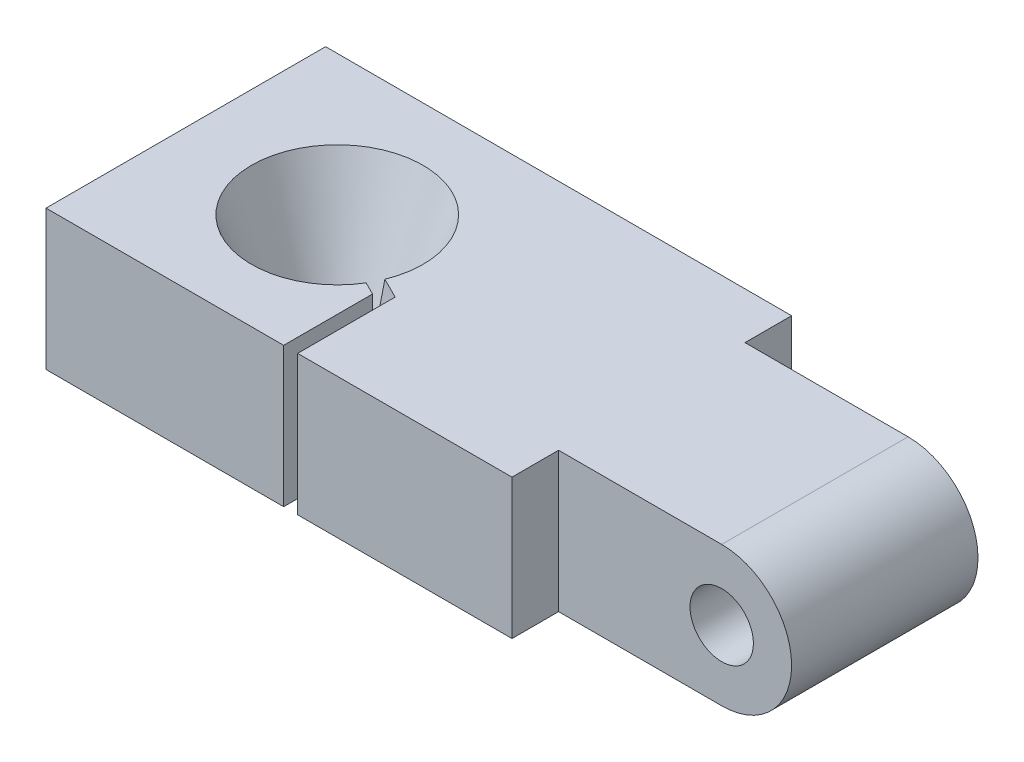
SolidWorks part; units mm, degrees
ref_plane "Front Plane" through (0, 0, 0) normal (0, 0, 1) x (1, 0, 0)
ref_plane "Top Plane" through (0, 0, 0) normal (0, 1, 0) x (1, 0, 0)
ref_plane "Right Plane" through (0, 0, 0) normal (1, 0, 0) x (0, 0, -1)
sketch "Sketch1" plane through (0, 0, 0) normal (0, 0, 1) x (1, 0, 0)
  line L1 (-17.145, -3.81) -> (17.145, -3.81)
  line L2 (-17.145, -3.81) -> (-17.145, 3.81)
  line L3 (-17.145, 3.81) -> (17.145, 3.81)
  line L4 (17.145, -3.81) -> (17.145, 3.81) construction
  line L5 (-17.145, -3.81) -> (17.145, 3.81) construction
  line L6 (-17.145, 3.81) -> (17.145, -3.81) construction
  arc A0 (17.145, 3.81) -> (17.145, -3.81) centre (17.145, 0) cw
  point P0 (0, 0)
  dimension "D1" = 7.62
  dimension "D2" = 34.29
extrude "Boss-Extrude1" add sketch "Sketch1" along normal blind 10.16
hole_wizard "#4 Clearance Hole1" positions "Sketch3" profile "Sketch2" hole size "#4" standard "ANSI Inch" end condition through all
sketch "Sketch3" plane through (0, 0, 10.16) normal (0, 0, 1) x (1, 0, 0)
  point P0 (17.145, 0)
sketch "Sketch2" plane through (17.145, 0, 10.16) normal (1, 0, 0) x (0, -1, 0)
  line L0 (0, 0) -> (0, 10.16)
  line L1 (0, 10.16) -> (1.7272, 10.16)
  line L2 (1.7272, 10.16) -> (1.7272, 0)
  line L5 (1.7272, 0) -> (0, 0)
  line L11 (0, -6.35) -> (0, 107.95) construction
  dimension "Thru Hole Dia." = 3.4544
  dimension "Thru Hole Depth" = 10.16
sketch "Sketch4" plane through (0, -3.81, 0) normal (0, 1, 0) x (1, 0, 0)
  line L0 (-17.145, -10.16) -> (-17.145, 0) construction
  circle A0 centre (-8.89, -5.08) radius 1.905
  point P0 (-8.89, -5.08)
  dimension "D2" = 3.81
  dimension "D1" = 8.255
extrude "Cut-Extrude1" cut sketch "Sketch4" along normal through all draft 20 draft outward yes
sketch "Sketch5" plane through (0, -3.81, 0) normal (0, -1, 0) x (1, 0, 0)
  circle A0 centre (-8.89, 5.08) radius 4.1275
  dimension "D1" = 8.255
extrude "Cut-Extrude2" cut sketch "Sketch5" against normal blind 1.27
sketch "Sketch6" plane through (0, -3.81, 0) normal (0, -1, 0) x (1, 0, 0)
  line L0 (-17.145, 5.08) -> (20.955, 5.08) construction
  line L1 (-17.145, 10.16) -> (8.255, 10.16)
  line L2 (-17.145, 10.16) -> (-17.145, 12.7)
  line L3 (-17.145, 12.7) -> (8.255, 12.7)
  line L4 (8.255, 10.16) -> (8.255, 12.7)
  line L5 (-17.145, 10.16) -> (-17.145, 0) construction
  line L6 (20.955, 0) -> (20.955, 10.16) construction
  line L7 (8.255, 0) -> (8.255, -2.54)
  line L8 (-17.145, -2.54) -> (8.255, -2.54)
  line L9 (-17.145, 0) -> (-17.145, -2.54)
  line L10 (-17.145, 0) -> (8.255, 0)
  dimension "D1" = 2.54
  dimension "D2" = 25.4
extrude "Boss-Extrude2" add sketch "Sketch6" against normal through all
sketch "Sketch8" plane through (0, 3.81, 0) normal (0, 1, 0) x (1, 0, 0)
  line L0 (-3.81, -12.7) -> (-3.81, -7.62) construction
  line L1 (8.255, -12.7) -> (-17.145, -12.7) construction
  line L2 (-3.81, -7.62) -> (-8.89, -5.08) construction
  line L3 (-3.429, -12.7) -> (-3.429, -7.3845)
  line L4 (-3.429, -7.3845) -> (-8.7196, -4.7392)
  line L5 (-4.191, -12.7) -> (-4.191, -7.8555)
  line L6 (-4.191, -7.8555) -> (-9.0604, -5.4208)
  line L7 (-9.0604, -5.4208) -> (-8.7196, -4.7392)
  line L8 (-4.191, -12.7) -> (-3.429, -12.7)
  dimension "D1" = 5.08
  dimension "D2" = 5.08
  dimension "D3" = 0.381
  dimension "D4" = 0.381
extrude "Cut-Extrude3" cut sketch "Sketch8" against normal through all
sketch "Sketch7" plane through (0, 3.81, 0) normal (0, 1, 0) x (1, 0, 0)
  line L1 (-17.145, 2.54) -> (8.255, 2.54) construction
  line L2 (17.145, -10.16) -> (17.145, 0) construction
  circle A0 centre (8.255, 2.54) radius 5.08
  circle A1 centre (-17.145, -12.7) radius 5.08
  circle A2 centre (-17.145, 2.54) radius 5.08
  circle A3 centre (8.255, -10.16) radius 5.08
  circle A4 centre (17.145, -5.08) radius 5.08
  dimension "D1" = 10.16
  dimension "D2" = 10.16
  dimension "D3" = 10.16
  dimension "D4" = 10.16
  dimension "D5" = 10.16
extrude "PrintTabs" [suppressed] add sketch "Sketch7" against normal blind 0.4
